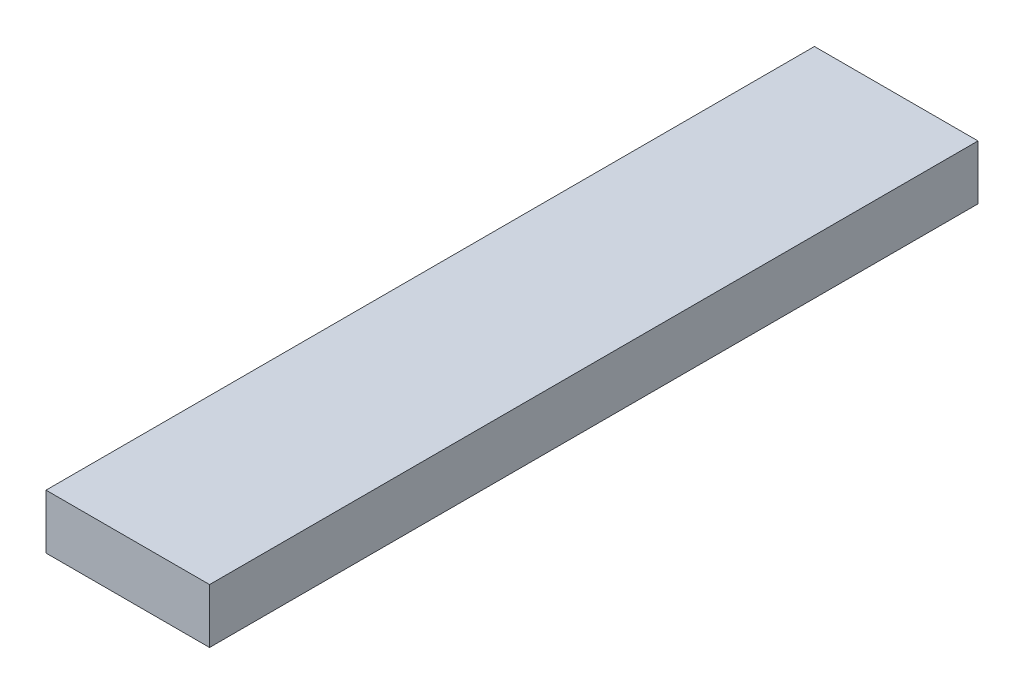
SolidWorks part; units mm, degrees
ref_plane "Front Plane" through (0, 0, 0) normal (0, 0, 1) x (1, 0, 0)
ref_plane "Top Plane" through (0, 0, 0) normal (0, 1, 0) x (1, 0, 0)
ref_plane "Right Plane" through (0, 0, 0) normal (1, 0, 0) x (0, 0, -1)
sketch "Sketch1" plane through (0, 0, 0) normal (0, 0, 1) x (1, 0, 0)
  line L1 (0, 0) -> (38.1, 0)
  line L2 (0, 0) -> (0, 12.7)
  line L3 (0, 12.7) -> (38.1, 12.7)
  line L4 (38.1, 0) -> (38.1, 12.7)
  dimension "D1" = 12.7
  dimension "D2" = 38.1
extrude "Boss-Extrude1" add sketch "Sketch1" along normal blind 179
